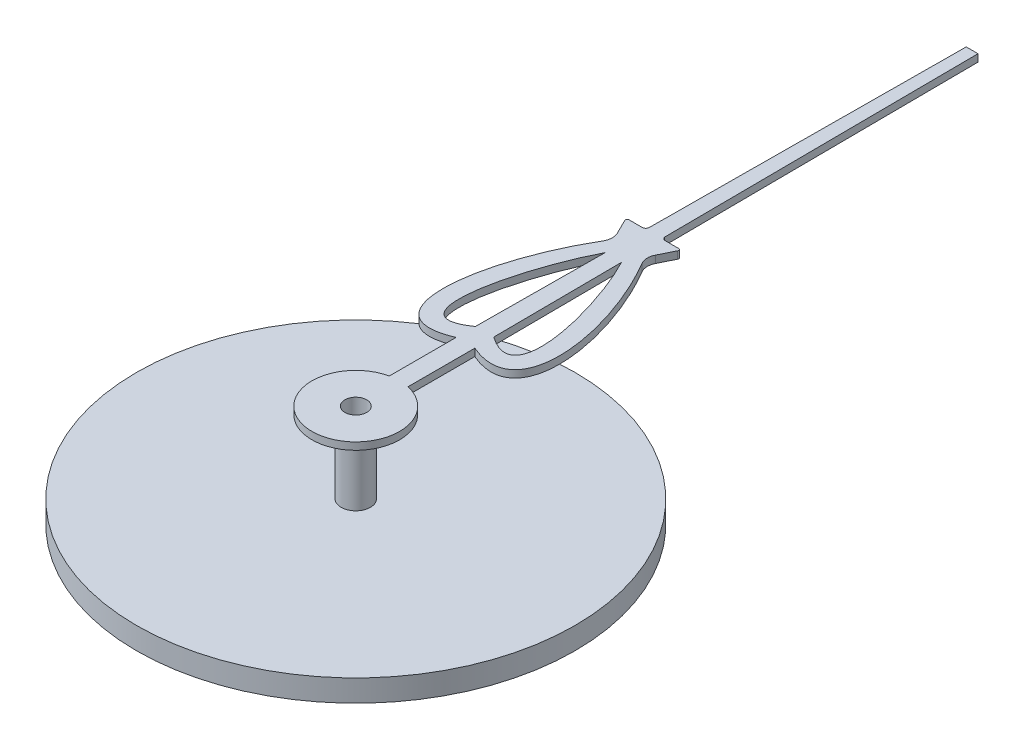
SolidWorks part; units mm, degrees
ref_plane "Front Plane" through (0, 0, 0) normal (0, 0, 1) x (1, 0, 0)
ref_plane "Top Plane" through (0, 0, 0) normal (0, 1, 0) x (1, 0, 0)
ref_plane "Right Plane" through (0, 0, 0) normal (1, 0, 0) x (0, 0, -1)
sketch "Sketch1" plane through (0, 0, 0) normal (0, 1, 0) x (1, 0, 0)
  line L0 (0, 8.4336) -> (0, -94.0328) construction
  line L1 (-2.0666, 0) -> (2.0487, 0) construction
  line L2 (-0.1276, 0.5863) -> (-0.1276, 1.501)
  line L4 (-0.3388, 4.0774) -> (-0.1574, 4.0774)
  line L5 (0.3595, 4.0396) -> (0.2601, 3.8392)
  line L6 (-0.3595, 4.0396) -> (-0.2601, 3.8392)
  line L7 (0.1276, 0.5863) -> (0.1276, 1.501)
  line L8 (0.3388, 4.0774) -> (0.1574, 4.0774)
  line L9 (-0.0805, 8.4336) -> (0.0807, 8.4336)
  line L10 (-0.1087, 4.1267) -> (-0.0805, 8.4336)
  line L11 (0.1099, 4.1159) -> (0.0807, 8.4336)
  line L12 (0.1139, 3.5225) -> (0.1258, 1.7615)
  line L13 (-0.1131, 3.5241) -> (-0.1257, 1.7616)
  arc A0 (-0.2601, 3.8392) -> (-0.2672, 3.6483) centre (-0.4393, 3.7503) cw
  arc A1 (-0.1574, 4.0774) -> (-0.1087, 4.1267) centre (-0.1579, 4.1266) ccw
  arc A2 (-0.3388, 4.0774) -> (-0.3595, 4.0396) centre (-0.3415, 4.0543) ccw
  arc A3 (-0.1276, 0.5863) -> (0.1276, 0.5863) centre (0, 0) ccw
  arc A4 (0.2601, 3.8392) -> (0.2672, 3.6483) centre (0.4393, 3.7503) ccw
  arc A5 (0.3388, 4.0774) -> (0.3595, 4.0396) centre (0.3415, 4.0543) cw
  arc A6 (0.1574, 4.0774) -> (0.1099, 4.1159) centre (0.1579, 4.1266) cw
  spline S0 degree 3 poles (-0.1276, 1.501) (-0.6136, 1.2927) (-0.9974, 1.8366) (-0.5812, 3.1185) (-0.2672, 3.6483) knots 0 0 0 0 0.463524 0.927047 0.927047 0.927047 0.927047
  spline S1 degree 3 poles (-0.1257, 1.7616) (-0.8914, 1.231) (-0.5009, 2.788) (-0.1131, 3.5241) knots 0.044188 0.044188 0.044188 0.044188 0.914543 0.914543 0.914543 0.914543
  spline S2 degree 3 poles (0.1258, 1.7615) (0.8908, 1.2315) (0.5014, 2.7857) (0.1139, 3.5225) knots 0.04423 0.04423 0.04423 0.04423 0.913901 0.913901 0.913901 0.913901
  spline S3 degree 3 poles (0.1276, 1.501) (1.0996, 1.0845) (0.8952, 2.5887) (0.2672, 3.6483) knots 0 0 0 0 0.927047 0.927047 0.927047 0.927047
  dimension "D1" = 0.2
  dimension "D4" = 1.2
extrude "Boss-Extrude1" add sketch "Sketch1" along normal blind 0.1
sketch "Sketch2" plane through (0, 0, 0) normal (0, -1, 0) x (1, 0, 0)
  circle A0 centre (0, 0) radius 0.2
  dimension "D1" = 0.4
extrude "Boss-Extrude2" add sketch "Sketch2" along normal blind 1
sketch "Sketch3" plane through (0, -1, 0) normal (0, -1, 0) x (1, 0, 0)
  circle A0 centre (0, 0) radius 3
  dimension "D1" = 6
extrude "Boss-Extrude3" add sketch "Sketch3" along normal blind 0.3
sketch "Sketch4" plane through (0, 0.1, 0) normal (0, 1, 0) x (1, 0, 0)
  circle A0 centre (0, 0) radius 0.15
  dimension "D1" = 0.3
extrude "Cut-Extrude1" cut sketch "Sketch4" against normal through all
